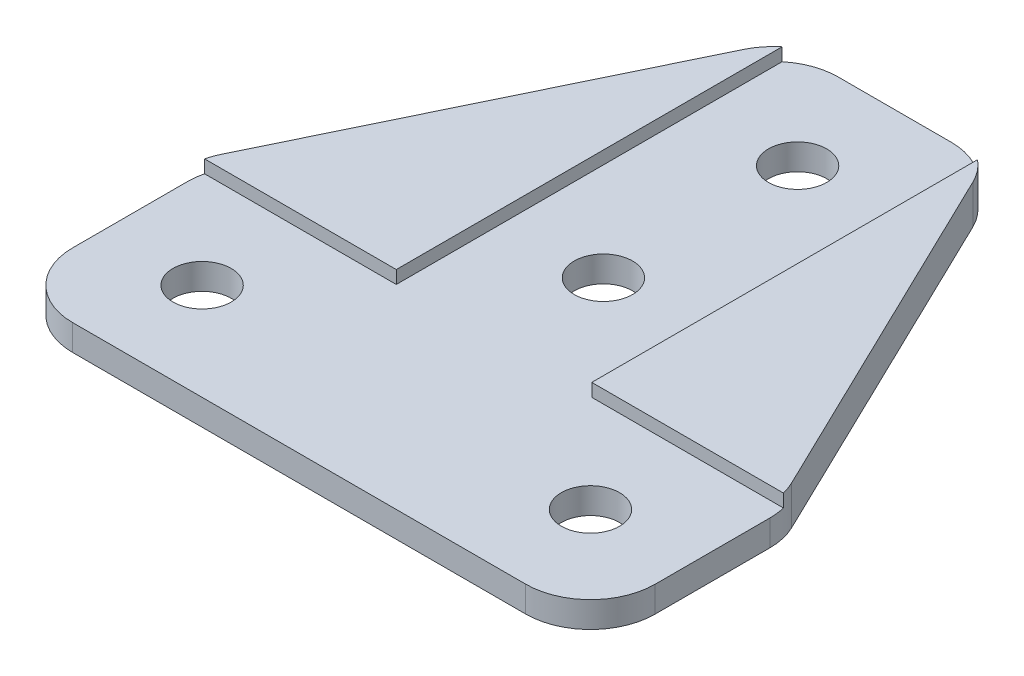
SolidWorks part; units mm, degrees
material "3.1305 (EN-AW 2117)"
ref_plane "正面" through (0, 0, 0) normal (0, 0, 1) x (1, 0, 0)
ref_plane "平面" through (0, 0, 0) normal (0, 1, 0) x (1, 0, 0)
ref_plane "右側面" through (0, 0, 0) normal (1, 0, 0) x (0, 0, -1)
sketch "ｽｹｯﾁ1" plane through (0, 0, 0) normal (0, 1, 0) x (1, 0, 0)
  line L0 (0, 0) -> (45, 0)
  line L1 (45, 0) -> (45, 15)
  line L2 (45, 15) -> (30, 46)
  line L3 (30, 46) -> (15, 46)
  line L4 (15, 46) -> (0, 15)
  line L5 (0, 15) -> (0, 0)
  dimension "D1" = 15
  dimension "D2" = 45
  dimension "D3" = 31
  dimension "D4" = 15
  dimension "D5" = 15
  dimension "D6" = 15
extrude "ﾎﾞｽ - 押し出し1" add sketch "ｽｹｯﾁ1" along normal blind 3
sketch "ｽｹｯﾁ2" plane through (0, 3, 0) normal (0, 1, 0) x (1, 0, 0)
  line L0 (0, 15) -> (0, 0) construction
  line L1 (0, 0) -> (45, 0) construction
  line L2 (45, 0) -> (45, 15) construction
  line L3 (30, 46) -> (15, 46) construction
  circle A0 centre (7.5, 7.5) radius 2.25
  circle A1 centre (22.5, 38.5) radius 2.25
  circle A2 centre (22.5, 23.5) radius 2.25
  circle A3 centre (37.5, 7.5) radius 2.25
  dimension "D1" = 22.5
  dimension "D2" = 22.5
  dimension "D3" = 7.5
  dimension "D4" = 7.5
  dimension "D5" = 7.5
  dimension "D7" = 4.5
  dimension "D8" = 4.5
  dimension "D9" = 4.5
  dimension "D10" = 4.5
  dimension "D11" = 7.5
  dimension "D6" = 7.5
  dimension "D13" = 15
extrude "ｶｯﾄ - 押し出し1" cut sketch "ｽｹｯﾁ2" against normal blind 3
fillet "ﾌｨﾚｯﾄ1" radius 5 6 edges at (30, 1.5, -46) (15, 1.5, -46) (45, 1.5, -15) (45, 1.5, 0) (0, 1.5, -15) (0, 1.5, 0)
sketch "ｽｹｯﾁ3" plane through (0, 3, 0) normal (0, 1, 0) x (1, 0, 0)
  line L0 (14.95, 46) -> (30.05, 46)
  line L1 (14.95, 46) -> (14.95, 15.05)
  line L2 (30.05, 46) -> (30.05, 15.05)
  line L3 (14.95, 15.05) -> (30.05, 15.05) construction
  line L4 (26.8648, 46) -> (18.1352, 46) construction
  line L5 (0, 0) -> (45, 0)
  line L6 (0, 0) -> (0, 15.05)
  line L7 (45, 0) -> (45, 15.05)
  line L8 (0, 15.05) -> (14.95, 15.05)
  line L9 (5, 0) -> (40, 0) construction
  line L10 (0, 13.8539) -> (0, 5) construction
  line L11 (45, 5) -> (45, 13.8539) construction
  line L12 (30.05, 15.05) -> (45, 15.05)
  line L13 (14.95, 15.05) -> (30.05, 15.05) construction
  point P17 (22.5, 46)
  point P18 (22.5, 46)
  dimension "D1" = 15.05
  dimension "D2" = 15.1
extrude "ｶｯﾄ - 押し出し2" cut sketch "ｽｹｯﾁ3" against normal blind 1
